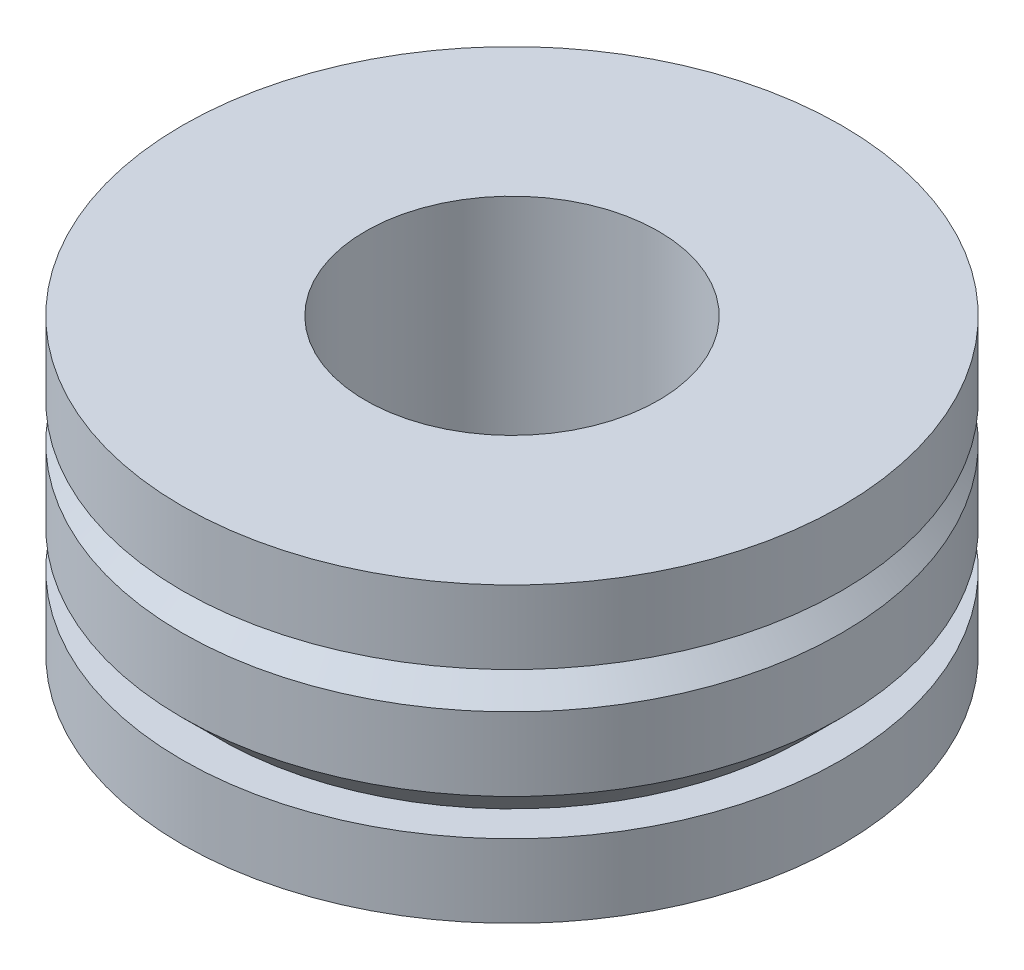
SolidWorks part; units mm, degrees
ref_plane "前视基准面" through (0, 0, 0) normal (0, 0, 1) x (1, 0, 0)
ref_plane "上视基准面" through (0, 0, 0) normal (0, 1, 0) x (1, 0, 0)
ref_plane "右视基准面" through (0, 0, 0) normal (1, 0, 0) x (0, 0, -1)
sketch "草图1" plane through (0, 0, 0) normal (0, 0, 1) x (1, 0, 0)
  line L0 (-85.5, 4) -> (-88, 4)
  line L1 (-88, 4) -> (-88, 0)
  line L2 (-88, 0) -> (-85.5, 0)
  line L3 (-85.5, 0) -> (-85.5, 1)
  line L4 (-85.5, 1) -> (-86, 1)
  line L5 (-86, 1) -> (-85.5, 1.5)
  line L6 (-85.5, 1.5) -> (-85.5, 2.5)
  line L7 (-85.5, 2.5) -> (-86, 3)
  line L8 (-86, 3) -> (-85.5, 3)
  line L9 (-85.5, 3) -> (-85.5, 4)
  line L10 (-90, 4) -> (-90, 0) construction
revolve "旋转1" add sketch "草图1" angle 360 about L10
